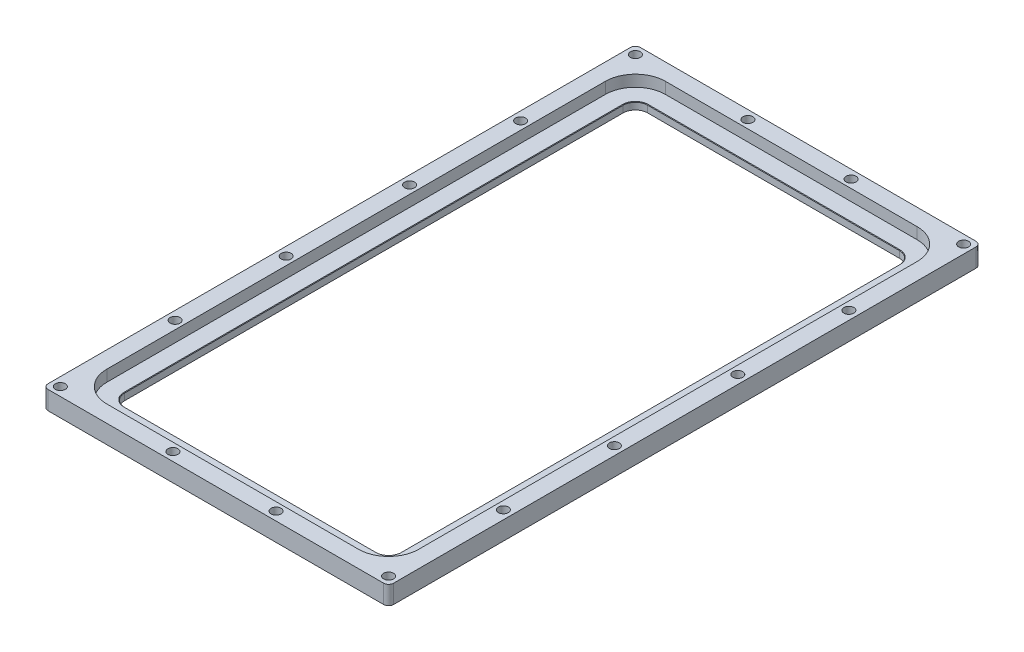
SolidWorks part; units mm, degrees
material "6061 Alloy"
ref_plane "Front Plane" through (0, 0, 0) normal (0, 0, 1) x (1, 0, 0)
ref_plane "Top Plane" through (0, 0, 0) normal (0, 1, 0) x (1, 0, 0)
ref_plane "Right Plane" through (0, 0, 0) normal (1, 0, 0) x (0, 0, -1)
sketch "Sketch1" plane through (0, 0, 0) normal (0, 1, 0) x (1, 0, 0)
  line L1 (0, 0) -> (177.8, 0)
  line L2 (0, 0) -> (0, 304.8)
  line L3 (0, 304.8) -> (177.8, 304.8)
  line L4 (177.8, 0) -> (177.8, 304.8)
  dimension "D1" = 177.8
  dimension "D2" = 304.8
extrude "Boss-Extrude1" add sketch "Sketch1" along normal blind 9.525
sketch "Sketch2" plane through (0, 9.525, 0) normal (0, 1, 0) x (1, 0, 0)
  line L20 (17.78, 17.78) -> (160.02, 17.78)
  line L21 (17.78, 287.02) -> (17.78, 17.78)
  line L22 (160.02, 17.78) -> (160.02, 287.02)
  line L23 (160.02, 287.02) -> (17.78, 287.02)
  line L24 (17.78, 17.78) -> (160.02, 17.78)
  line L25 (17.78, 287.02) -> (17.78, 17.78)
  line L26 (160.02, 17.78) -> (160.02, 287.02)
  line L27 (160.02, 287.02) -> (17.78, 287.02)
  dimension "D1" = 17.78
extrude "Cut-Extrude1" cut sketch "Sketch2" against normal through all
sketch "Sketch3" plane through (0, 9.525, 0) normal (0, 1, 0) x (1, 0, 0)
  line L0 (88.9, 304.8) -> (88.9, 0) construction
  line L1 (177.8, 304.8) -> (0, 304.8) construction
  line L2 (0, 0) -> (177.8, 0) construction
  line L3 (177.8, 152.4) -> (0, 152.4) construction
  line L4 (177.8, 0) -> (177.8, 304.8) construction
  line L5 (0, 304.8) -> (0, 0) construction
  line L6 (0, 300.355) -> (177.8, 300.355) construction
  line L7 (4.445, 304.8) -> (4.445, 152.4) construction
  circle A0 centre (4.445, 184.15) radius 2.5527
  circle A1 centre (4.445, 241.3) radius 2.5527
  circle A2 centre (62.357, 300.355) radius 2.5527
  circle A3 centre (4.445, 300.355) radius 2.5527
  circle A4 centre (173.355, 184.15) radius 2.5527
  circle A5 centre (173.355, 241.3) radius 2.5527
  circle A6 centre (173.355, 300.355) radius 2.5527
  circle A7 centre (115.443, 300.355) radius 2.5527
  circle A8 centre (173.355, 120.65) radius 2.5527
  circle A9 centre (173.355, 63.5) radius 2.5527
  circle A10 centre (173.355, 4.445) radius 2.5527
  circle A11 centre (115.443, 4.445) radius 2.5527
  circle A12 centre (62.357, 4.445) radius 2.5527
  circle A13 centre (4.445, 4.445) radius 2.5527
  circle A14 centre (4.445, 63.5) radius 2.5527
  circle A15 centre (4.445, 120.65) radius 2.5527
  dimension "D3" = 5.1054
  dimension "D1" = 4.445
  dimension "D2" = 4.445
  dimension "D4" = 57.912
  dimension "D5" = 31.75
  dimension "D6" = 88.9
extrude "Cut-Extrude2" cut sketch "Sketch3" against normal through all
fillet "Fillet4" radius 6.35 4 edges at (17.78, 4.7625, -287.02) (17.78, 4.7625, -17.78) (160.02, 4.7625, -287.02) (160.02, 4.7625, -17.78)
sketch "Sketch7" plane through (0, 9.525, 0) normal (0, 1, 0) x (1, 0, 0)
  line L0 (24.13, 17.78) -> (153.67, 17.78) construction
  line L1 (160.02, 24.13) -> (160.02, 280.67) construction
  line L2 (153.67, 287.02) -> (24.13, 287.02) construction
  line L3 (17.78, 280.67) -> (17.78, 24.13) construction
  line L4 (24.13, 17.78) -> (153.67, 17.78)
  line L5 (160.02, 24.13) -> (160.02, 280.67)
  line L6 (153.67, 287.02) -> (24.13, 287.02)
  line L7 (17.78, 280.67) -> (17.78, 24.13)
  line L8 (8.636, 280.67) -> (8.636, 24.13)
  line L9 (24.13, 8.636) -> (153.67, 8.636)
  line L10 (169.164, 24.13) -> (169.164, 280.67)
  line L11 (153.67, 296.164) -> (24.13, 296.164)
  arc A0 (17.78, 24.13) -> (24.13, 17.78) centre (24.13, 24.13) ccw construction
  arc A1 (153.67, 17.78) -> (160.02, 24.13) centre (153.67, 24.13) ccw construction
  arc A2 (160.02, 280.67) -> (153.67, 287.02) centre (153.67, 280.67) ccw construction
  arc A3 (24.13, 287.02) -> (17.78, 280.67) centre (24.13, 280.67) ccw construction
  arc A4 (17.78, 24.13) -> (24.13, 17.78) centre (24.13, 24.13) ccw
  arc A5 (153.67, 17.78) -> (160.02, 24.13) centre (153.67, 24.13) ccw
  arc A6 (160.02, 280.67) -> (153.67, 287.02) centre (153.67, 280.67) ccw
  arc A7 (24.13, 287.02) -> (17.78, 280.67) centre (24.13, 280.67) ccw
  arc A8 (8.636, 24.13) -> (24.13, 8.636) centre (24.13, 24.13) ccw
  arc A9 (153.67, 8.636) -> (169.164, 24.13) centre (153.67, 24.13) ccw
  arc A10 (169.164, 280.67) -> (153.67, 296.164) centre (153.67, 280.67) ccw
  arc A11 (24.13, 296.164) -> (8.636, 280.67) centre (24.13, 280.67) ccw
  dimension "D1" = 9.144
extrude "Cut-Extrude5" cut sketch "Sketch7" against normal blind 5.842
chamfer "Chamfer1" distance 0.254 angle 45 8 edges at (19.6399, 3.683, -19.6399) (88.9, 3.683, -17.78) (158.1601, 3.683, -19.6399) (160.02, 3.683, -152.4) (158.1601, 3.683, -285.1601) (88.9, 3.683, -287.02) (19.6399, 3.683, -285.1601) (17.78, 3.683, -152.4)
fillet "Fillet5" radius 2.54 4 edges at (0, 4.7625, -304.8) (177.8, 4.7625, -304.8) (177.8, 4.7625, 0) (0, 4.7625, 0)
